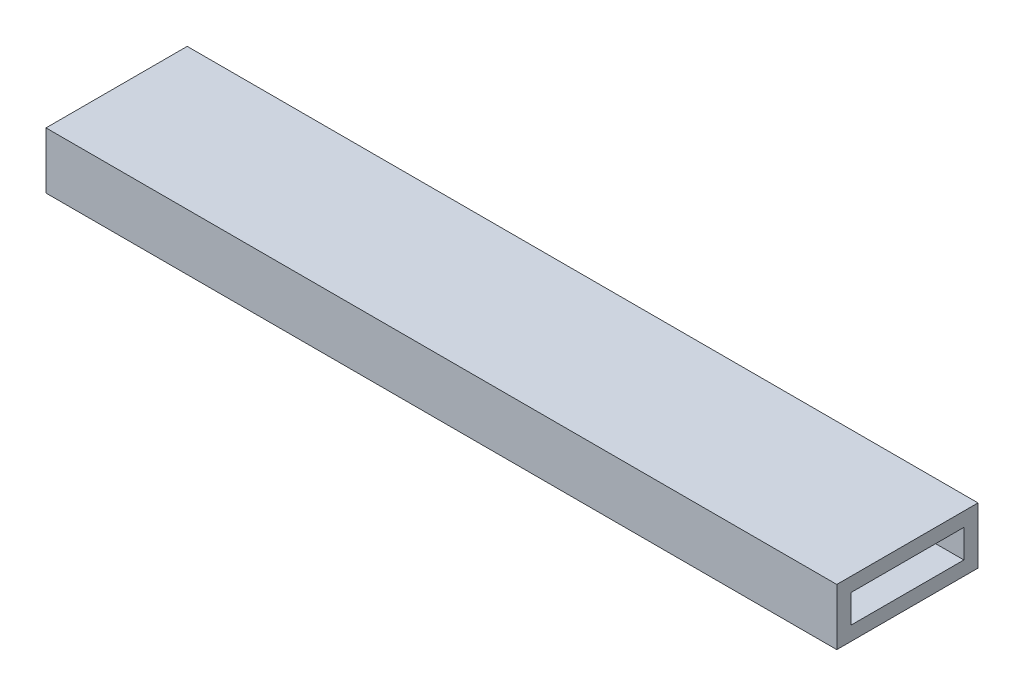
SolidWorks part; units mm, degrees
ref_plane "Front Plane" through (0, 0, 0) normal (0, 0, 1) x (1, 0, 0)
ref_plane "Top Plane" through (0, 0, 0) normal (0, 1, 0) x (1, 0, 0)
ref_plane "Right Plane" through (0, 0, 0) normal (1, 0, 0) x (0, 0, -1)
sketch "Sketch1" plane through (0, 0, 0) normal (1, 0, 0) x (0, 0, -1)
  line L1 (0, 0) -> (100, 0)
  line L2 (0, 0) -> (0, 40)
  line L3 (0, 40) -> (100, 40)
  line L4 (100, 0) -> (100, 40)
  line L5 (10, 10) -> (90, 10)
  line L6 (10, 10) -> (10, 30)
  line L7 (10, 30) -> (90, 30)
  line L8 (90, 10) -> (90, 30)
  dimension "D1" = 40
  dimension "D2" = 100
  dimension "D3" = 10
  dimension "D4" = 10
  dimension "D5" = 10
  dimension "D6" = 10
extrude "Boss-Extrude1" add sketch "Sketch1" along normal blind 560
